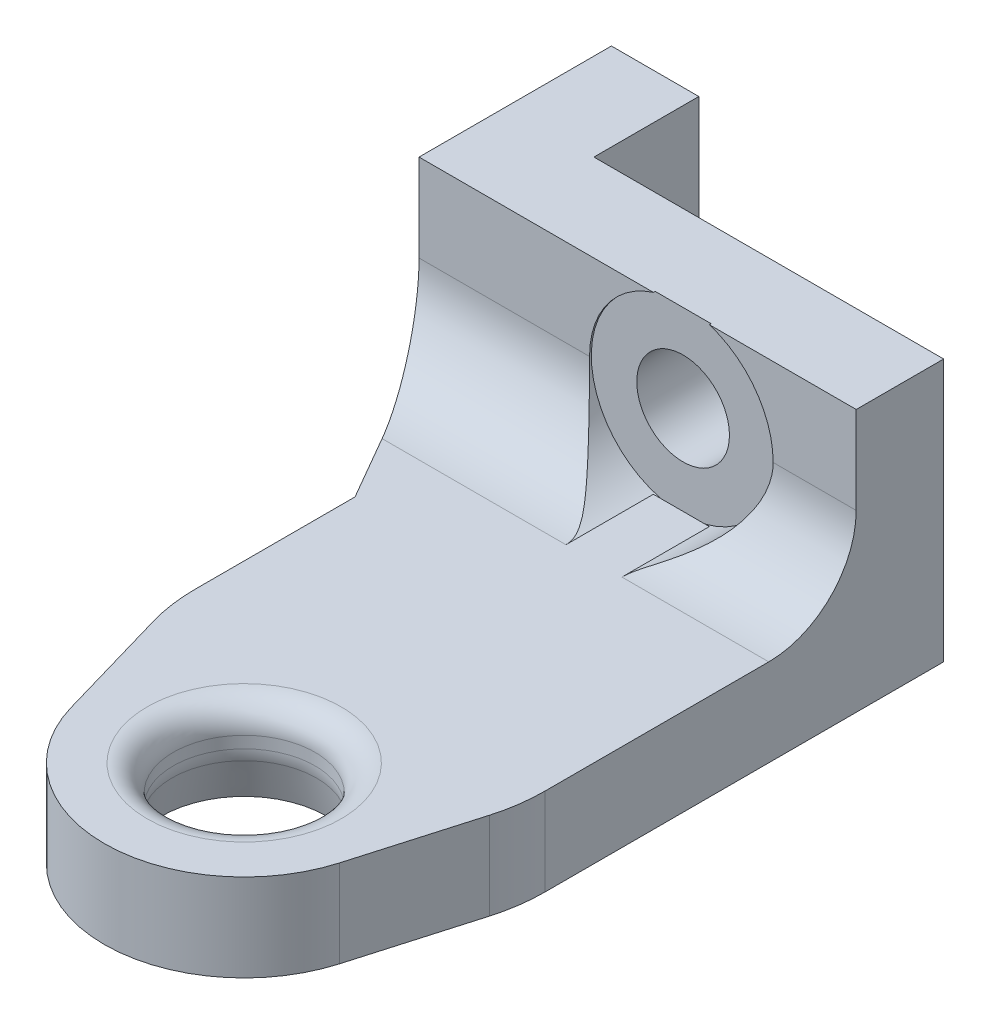
SolidWorks part; units mm, degrees
ref_plane "Front Plane" through (0, 0, 0) normal (0, 0, 1) x (1, 0, 0)
ref_plane "Top Plane" through (0, 0, 0) normal (0, 1, 0) x (1, 0, 0)
ref_plane "Right Plane" through (0, 0, 0) normal (1, 0, 0) x (0, 0, -1)
ref_plane "Plane1" through (0, 5, 0) normal (0, 1, 0) x (1, 0, 0)
sketch "Sketch1" plane through (0, 5, 0) normal (0, 1, 0) x (1, 0, 0)
  line L0 (10, 5.7759) -> (10, 36)
  line L1 (10, 36) -> (-15, 36)
  line L2 (-15, 36) -> (-15, 25)
  line L3 (-15, 25) -> (-10, 16.3397)
  line L4 (-10, 16.3397) -> (-10, 5.7759)
  line L5 (-10, 5.7759) -> (-7.6846, -2.2241)
  line L6 (7.6846, -2.2241) -> (10, 5.7759)
  arc A0 (-7.6846, -2.2241) -> (7.6846, -2.2241) centre (0, 0) ccw
extrude "Boss-Extrude1" add sketch "Sketch1" against normal blind 5
sketch "Sketch2" plane through (0, 5, 0) normal (0, 1, 0) x (-1, 0, 0)
  line L0 (-10, -25) -> (15, -25)
  line L1 (15, -25) -> (15, -36)
  line L2 (15, -36) -> (-10, -36)
  line L3 (-10, -36) -> (-10, -25)
extrude "Boss-Extrude2" add sketch "Sketch2" along normal blind 10
sketch "Sketch3" plane through (0, 0, 0) normal (0, -1, 0) x (1, 0, 0)
  line L0 (-10, -30) -> (-10, -36)
  line L1 (-10, -36) -> (10, -36)
  line L2 (10, -36) -> (10, -30)
  line L3 (10, -30) -> (-10, -30)
extrude "Cut-Extrude1" cut sketch "Sketch3" against normal through all
hole_wizard "Ø8.1 (8.1) Diameter Hole1" positions "Sketch7" profile "Sketch6" hole size "Ø8.1" standard "ANSI Metric"
sketch "Sketch7" plane through (0, 0, 0) normal (0, -1, 0) x (-1, 0, 0)
  point P0 (0, 0)
sketch "Sketch6" plane through (0, 0, 0) normal (1, 0, 0) x (0, 0, -1)
  line L0 (0, 0) -> (0, 15)
  line L1 (0, 15) -> (4.05, 15)
  line L2 (4.05, 15) -> (4.05, 2.5)
  line L3 (4.05, 2.5) -> (4.7199, 0)
  line L5 (4.7199, 0) -> (0, 0)
  line L6 (-4.05, 2.5) -> (-4.7199, 0) construction
  line L11 (0, -6.35) -> (0, 107.95) construction
  dimension "Thru Hole Dia." = 8.1
  dimension "Thru Hole Depth" = 15
  dimension "Near C'Sink Dia." = 9.4397
  dimension "Near C'Sink Angle" = 30
hole_wizard "CBORE for M5 SBHCS1" positions "Sketch5" profile "Sketch4" counterbore size "M5" standard "ANSI Metric"
sketch "Sketch5" plane through (0, 0, -25) normal (0, 0, 1) x (1, 0, 0)
  point P0 (0, 10)
sketch "Sketch4" plane through (0, 10, -25) normal (1, 0, 0) x (0, -1, 0)
  line L0 (0, 0) -> (0, 11)
  line L1 (0, 11) -> (2.65, 11)
  line L3 (2.65, 11) -> (2.65, 0.1)
  line L4 (2.65, 0.1) -> (5.25, 0.1)
  line L5 (5.25, 0.1) -> (5.25, 0)
  line L7 (5.25, 0) -> (0, 0)
  line L11 (0, -6.35) -> (0, 107.95) construction
  dimension "Thru Hole Dia." = 5.3
  dimension "Thru Hole Depth" = 11
  dimension "C'Bore Dia." = 10.5
  dimension "C'Bore Depth" = 0.1
fillet "Fillet1" radius 1.5 1 edges at (0, 5, 4.05)
fillet "Fillet2" radius 2.5 1 edges at (0, 2.5, -4.05)
fillet "Fillet3" radius 5 2 edges at (-8.3004, 5, -25) (5.8004, 5, -25)
fillet "Fillet4" radius 10 2 edges at (10, 2.5, -5.7759) (-10, 2.5, -5.7759)
